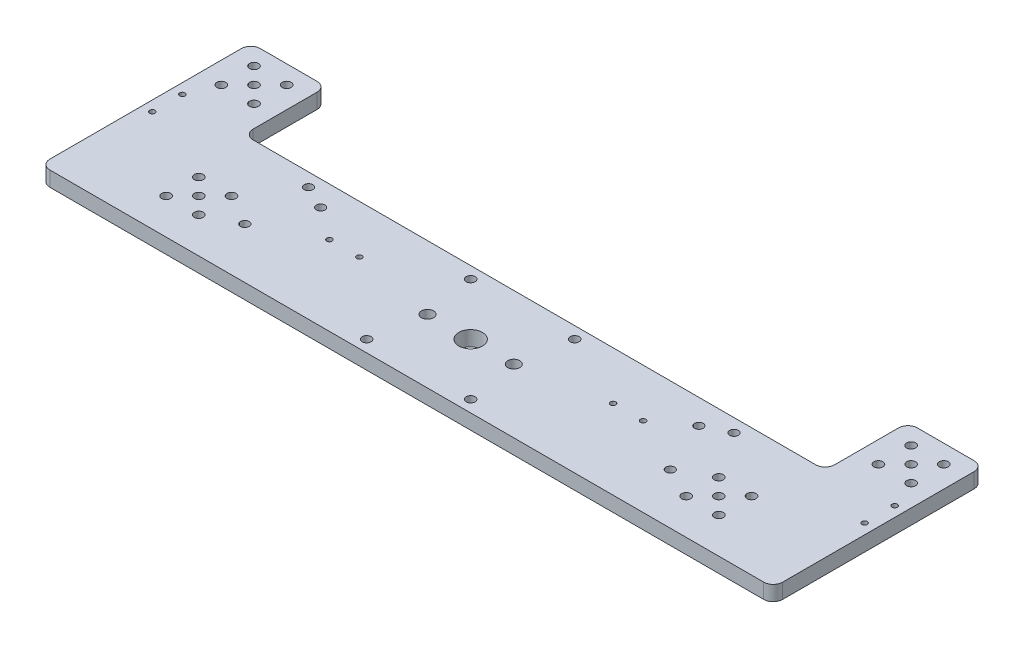
SolidWorks part; units mm, degrees
ref_plane "Front Plane" through (0, 0, 0) normal (0, 0, 1) x (1, 0, 0)
ref_plane "Top Plane" through (0, 0, 0) normal (0, 1, 0) x (1, 0, 0)
ref_plane "Right Plane" through (0, 0, 0) normal (1, 0, 0) x (0, 0, -1)
sketch "Sketch1" plane through (0, 0, 0) normal (0, 1, 0) x (1, 0, 0)
  line L1 (-155, -27) -> (155, -27)
  line L2 (-155, -27) -> (-155, 27)
  line L3 (-123, 27) -> (123, 27)
  line L4 (155, -27) -> (155, 27)
  line L5 (-155, -27) -> (155, 27) construction
  line L6 (-155, 27) -> (155, -27) construction
  line L7 (-123, 62) -> (-155, 62)
  line L8 (-123, 62) -> (-123, 27)
  line L10 (-155, 62) -> (-155, 27)
  line L11 (-123, 62) -> (-155, 27) construction
  line L12 (-123, 27) -> (-155, 62) construction
  line L13 (123, 62) -> (155, 62)
  line L14 (123, 62) -> (123, 27)
  line L16 (155, 62) -> (155, 27)
  line L17 (123, 62) -> (155, 27) construction
  line L18 (123, 27) -> (155, 62) construction
  point P0 (0, 0)
  point P6 (-139, 44.5)
  point P7 (139, 44.5)
  dimension "D1" = 310
  dimension "D2" = 32
  dimension "D3" = 35
  dimension "D4" = 54
extrude "Boss-Extrude1" add sketch "Sketch1" along normal blind 6.35
sketch "Sketch2" plane through (0, 6.35, 0) normal (0, 1, 0) x (1, 0, 0)
  circle A0 centre (0, 0) radius 5
  dimension "D1" = 10
extrude "Cut-Extrude1" cut sketch "Sketch2" against normal through all
sketch "Sketch3" plane through (0, 6.35, 0) normal (0, 1, 0) x (1, 0, 0)
  line L0 (-110, -5) -> (110, -5) construction
  line L1 (22, -22) -> (-22, -22) construction
  line L2 (22, -22) -> (22, 22) construction
  line L3 (22, 22) -> (-22, 22) construction
  line L4 (-22, -22) -> (-22, 22) construction
  line L5 (22, -22) -> (-22, 22) construction
  line L6 (22, 22) -> (-22, -22) construction
  line L7 (-116.915, -11.915) -> (-103.085, -11.915) construction
  line L8 (-116.915, -11.915) -> (-116.915, 1.915) construction
  line L9 (-116.915, 1.915) -> (-103.085, 1.915) construction
  line L10 (-103.085, -11.915) -> (-103.085, 1.915) construction
  line L11 (-116.915, -11.915) -> (-103.085, 1.915) construction
  line L12 (-116.915, 1.915) -> (-103.085, -11.915) construction
  line L13 (116.915, -11.915) -> (103.085, -11.915) construction
  line L14 (116.915, -11.915) -> (116.915, 1.915) construction
  line L15 (116.915, 1.915) -> (103.085, 1.915) construction
  line L16 (103.085, -11.915) -> (103.085, 1.915) construction
  line L17 (116.915, -11.915) -> (103.085, 1.915) construction
  line L18 (116.915, 1.915) -> (103.085, -11.915) construction
  line L19 (-145.915, 40.435) -> (-132.085, 40.435) construction
  line L20 (-145.915, 40.435) -> (-145.915, 54.265) construction
  line L21 (-145.915, 54.265) -> (-132.085, 54.265) construction
  line L22 (-132.085, 40.435) -> (-132.085, 54.265) construction
  line L23 (-145.915, 40.435) -> (-132.085, 54.265) construction
  line L24 (-145.915, 54.265) -> (-132.085, 40.435) construction
  line L25 (132.085, 40.435) -> (145.915, 40.435) construction
  line L26 (132.085, 40.435) -> (132.085, 54.265) construction
  line L27 (132.085, 54.265) -> (145.915, 54.265) construction
  line L28 (145.915, 40.435) -> (145.915, 54.265) construction
  line L29 (132.085, 40.435) -> (145.915, 54.265) construction
  line L30 (132.085, 54.265) -> (145.915, 40.435) construction
  line L31 (-139, 47.35) -> (139, 47.35) construction
  point P0 (0, 0)
  point P6 (-110, -5)
  point P11 (110, -5)
  point P16 (-139, 47.35)
  point P21 (139, 47.35)
  point P26 (0, -5)
  point P32 (0, 47.35)
  dimension "D1" = 44
  dimension "D2" = 44
  dimension "D3" = 13.83
  dimension "D4" = 220
  dimension "D5" = 278
  dimension "D6" = 52.35
  dimension "D7" = 5
hole_wizard "#6 Clearance Hole1" positions "3DSketch2" profile "Sketch4" hole size "#6" standard "ANSI Inch"
sketch3d "3DSketch2"
  point P0 (-145.915, 6.35, -54.265)
  point P3 (-132.085, 6.35, -54.265)
  point P6 (-132.085, 6.35, -40.435)
  point P9 (-145.915, 6.35, -40.435)
  point P12 (-139, 6.35, -47.35)
  point P15 (-116.915, 6.35, -1.915)
  point P18 (-103.085, 6.35, -1.915)
  point P21 (-103.085, 6.35, 11.915)
  point P24 (-116.915, 6.35, 11.915)
  point P27 (-110, 6.35, 5)
  point P30 (-22, 6.35, -22)
  point P33 (22, 6.35, -22)
  point P36 (22, 6.35, 22)
  point P39 (-22, 6.35, 22)
  point P42 (103.085, 6.35, 11.915)
  point P45 (103.085, 6.35, -1.915)
  point P48 (116.915, 6.35, -1.915)
  point P51 (116.915, 6.35, 11.915)
  point P54 (110, 6.35, 5)
  point P57 (132.085, 6.35, -40.435)
  point P60 (139, 6.35, -47.35)
  point P63 (132.085, 6.35, -54.265)
  point P66 (145.915, 6.35, -54.265)
  point P69 (145.915, 6.35, -40.435)
sketch "Sketch4" plane through (-145.915, 6.35, -54.265) normal (1, 0, 0) x (0, 0, 1)
  line L0 (0, 0) -> (0, 11.1408)
  line L1 (0, 11.1408) -> (1.8986, 10)
  line L2 (1.8986, 10) -> (1.8986, 0)
  line L5 (1.8986, 0) -> (0, 0)
  line L10 (0, 11.1408) -> (-1.8987, 10) construction
  line L11 (0, -6.35) -> (0, 107.95) construction
  dimension "Hole Dia." = 3.7973
  dimension "Hole Depth" = 10
  dimension "Drill Angle" = 118
fillet "Fillet1" radius 4 8 edges at (155, 3.175, 27) (155, 3.175, -62) (123, 3.175, -62) (123, 3.175, -27) (-123, 3.175, -27) (-155, 3.175, 27) (-123, 3.175, -62) (-155, 3.175, -62)
sketch "Sketch5" plane through (0, 6.35, 0) normal (0, 1, 0) x (1, 0, 0)
  line L0 (-18.25, 0) -> (18.25, 0) construction
  point P5 (0, 0)
  dimension "D1" = 36.5
hole_wizard "#10 Clearance Hole1" positions "3DSketch3" profile "Sketch6" hole size "#10" standard "ANSI Inch"
sketch3d "3DSketch3"
  point P0 (-18.25, 6.35, 0)
  point P3 (18.25, 6.35, 0)
sketch "Sketch6" plane through (-18.25, 6.35, 0) normal (1, 0, 0) x (0, 0, 1)
  line L0 (0, 0) -> (0, 11.5338)
  line L1 (0, 11.5338) -> (2.5527, 10)
  line L2 (2.5527, 10) -> (2.5527, 0)
  line L5 (2.5527, 0) -> (0, 0)
  line L10 (0, 11.5338) -> (-2.5527, 10) construction
  line L11 (0, -6.35) -> (0, 107.95) construction
  dimension "Hole Dia." = 5.1054
  dimension "Hole Depth" = 10
  dimension "Drill Angle" = 118
sketch "Sketch7" plane through (0, 6.35, 0) normal (0, 1, 0) x (1, 0, 0)
  line L0 (119, 27) -> (-119, 27) construction
  line L1 (-90, 21.412) -> (90, 21.412) construction
  line L2 (-90, 21.412) -> (-90, -5.5374) construction
  line L3 (-90, -5.5374) -> (90, -5.5374) construction
  line L4 (90, 21.412) -> (90, -5.5374) construction
  line L5 (-90, 21.412) -> (90, -5.5374) construction
  line L6 (-90, -5.5374) -> (90, 21.412) construction
  line L7 (-80, 16.5352) -> (80, 16.5352) construction
  point P0 (0, 7.9373)
  point P12 (0, 16.5352)
  dimension "D1" = 26.9494
  dimension "D2" = 5.588
  dimension "D3" = 180
  dimension "D4" = 160
  dimension "D5" = 10.4648
hole_wizard "#6 Clearance Hole2" positions "Sketch8" profile "Sketch9" hole size "#6" standard "ANSI Inch" end condition through all
sketch "Sketch8" plane through (0, 6.35, 0) normal (0, 1, 0) x (-1, 0, 0)
  point P0 (90, -21.412)
  point P3 (90, 5.5374)
  point P6 (-90, 5.5374)
  point P9 (-90, -21.412)
  point P13 (80, -16.5352)
  point P16 (-80, -16.5352)
sketch "Sketch9" plane through (-90, 6.35, -21.412) normal (1, 0, 0) x (0, 0, 1)
  line L0 (0, 0) -> (0, 6.35)
  line L1 (0, 6.35) -> (1.8288, 6.35)
  line L2 (1.8288, 6.35) -> (1.8288, 0)
  line L5 (1.8288, 0) -> (0, 0)
  line L11 (0, -6.35) -> (0, 107.95) construction
  dimension "Thru Hole Dia." = 3.6576
  dimension "Thru Hole Depth" = 6.35
sketch "Sketch10" plane through (0, 6.35, 0) normal (0, 1, 0) x (1, 0, 0)
  line L0 (-150.684, 28.7) -> (-150.684, 16) construction
  line L2 (-66.35, 6.609) -> (-53.65, 6.609) construction
  circle A0 centre (-139, 47.35) radius 1.8987 construction
  circle A1 centre (-110, -5) radius 1.8987 construction
  point P3 (-150.684, 22.35)
  point P9 (-60, 6.609)
  dimension "D2" = 11.684
  dimension "D5" = 11.609
  dimension "D1" = 12.7
  dimension "D3" = 25
  dimension "D4" = 12.7
  dimension "D6" = 60
hole_wizard "Tap Drill for #4-40 Tap1" positions "3DSketch4" profile "Sketch11" hole size "#4-40" standard "ANSI Inch"
sketch3d "3DSketch4"
  point P0 (-150.684, 6.35, -28.7)
  point P3 (-150.684, 6.35, -16)
  point P6 (-66.35, 6.35, -6.609)
  point P9 (-53.65, 6.35, -6.609)
sketch "Sketch11" plane through (-150.684, 6.35, -28.7) normal (1, 0, 0) x (0, 0, 1)
  line L0 (0, 0) -> (0, 7.0292)
  line L1 (0, 7.0292) -> (1.1303, 6.35)
  line L2 (1.1303, 6.35) -> (1.1303, 0)
  line L5 (1.1303, 0) -> (0, 0)
  line L10 (0, 7.0292) -> (-1.1303, 6.35) construction
  line L11 (0, -6.35) -> (0, 107.95) construction
  dimension "Hole Dia." = 2.2606
  dimension "Hole Depth" = 6.35
  dimension "Drill Angle" = 118
mirror "Mirror1" about plane through (0, 0, 0) normal (1, 0, 0) of "Tap Drill for #4-40 Tap1"
